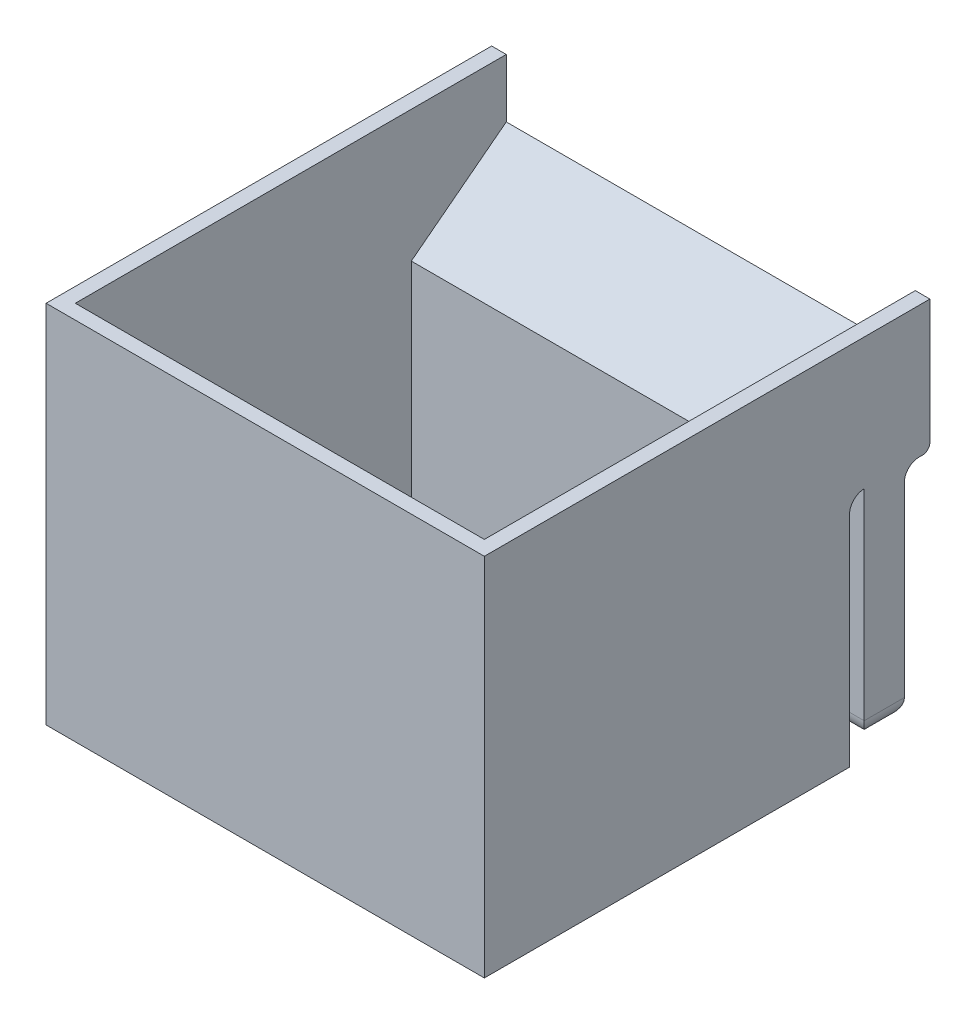
SolidWorks part; units mm, degrees
ref_plane "前基準面" through (0, 0, 0) normal (0, 0, 1) x (1, 0, 0)
ref_plane "上基準面" through (0, 0, 0) normal (0, 1, 0) x (1, 0, 0)
ref_plane "右基準面" through (0, 0, 0) normal (1, 0, 0) x (0, 0, -1)
sketch "草圖1" plane through (0, 0, 0) normal (1, 0, 0) x (0, 0, -1)
  line L0 (-42.2544, 29.5336) -> (-42.2544, -20.4664)
  line L1 (-42.2544, -20.4664) -> (7.7456, -20.4664)
  line L2 (7.7456, -20.4664) -> (7.7456, 11.5336)
  line L3 (7.7456, 11.5336) -> (18.7456, 11.5336)
  line L4 (18.7456, 11.5336) -> (18.7456, 21.5336)
  line L6 (5.7456, 11.5336) -> (5.7456, -18.4664)
  line L7 (5.7456, -18.4664) -> (-40.2544, -18.4664)
  line L8 (-40.2544, -18.4664) -> (-40.2544, 29.5336)
  line L9 (-40.2544, 29.5336) -> (-42.2544, 29.5336)
  line L10 (18.7456, 21.5336) -> (5.7456, 11.5336)
  dimension "D1" = 32
  dimension "D2" = 50
  dimension "D3" = 50
  dimension "D4" = 10
  dimension "D5" = 11
  dimension "D6" = 2
  dimension "D7" = 2
  dimension "D8" = 2
extrude "填料-伸長1" add sketch "草圖1" along normal blind 60
fillet "圓角1" radius 2 1 edges at (30, 11.5336, -7.7456)
sketch "草圖2" plane through (0, 11.5336, 0) normal (0, -1, 0) x (1, 0, 0)
  line L0 (60, -9.7456) -> (60, -18.7456) construction
  line L1 (0, -9.7456) -> (60, -9.7456)
  line L2 (0, -9.7456) -> (0, -15.2456)
  line L3 (0, -15.2456) -> (60, -15.2456)
  line L4 (60, -9.7456) -> (60, -15.2456)
  dimension "D1" = 5.5
extrude "填料-伸長2" add sketch "草圖2" along normal blind 30 contours L2 L1 L4 L3
fillet "圓角3" radius 2 1 edges at (30, 11.5336, -15.2456)
sketch "草圖3" plane through (0, -18.4664, 0) normal (0, 1, 0) x (1, 0, 0)
  line L0 (0, -27.5) -> (0, 27.5) construction
  line L1 (0, 5.7456) -> (2, 5.7456)
  line L2 (0, 5.7456) -> (0, -40.2544)
  line L3 (0, -40.2544) -> (2, -40.2544)
  line L4 (2, 5.7456) -> (2, -40.2544)
  line L5 (60, 5.7456) -> (0, 5.7456) construction
  line L6 (60, -40.2544) -> (0, -40.2544) construction
  line L8 (60, 5.7456) -> (58, 5.7456)
  line L9 (60, 5.7456) -> (60, -40.2544)
  line L10 (60, -40.2544) -> (58, -40.2544)
  line L11 (58, 5.7456) -> (58, -40.2544)
  line M3 (0, 5.7456) -> (0, -40.2544)
  line M4 (0, -40.2544) -> (60, -40.2544)
  line M5 (60, -40.2544) -> (60, 5.7456)
  line M6 (60, 5.7456) -> (0, 5.7456)
  dimension "D1" = 2
  dimension "D2" = 2
extrude "填料-伸長3" add sketch "草圖3" along normal blind 48 contours L4 M6 M3 M4 | L11 M6 M4 M5
sketch "草圖4" plane through (0, 0, -5.7456) normal (0, 0, -1) x (-1, 0, 0)
  line L0 (0, 27.5) -> (0, -27.5) construction
  line L1 (-2, 29.5336) -> (0, 29.5336)
  line L2 (-2, 29.5336) -> (-2, 11.5336)
  line L3 (-2, 11.5336) -> (0, 11.5336)
  line L4 (0, 29.5336) -> (0, 11.5336)
  dimension "D1" = 18
extrude "填料-伸長4" add sketch "草圖4" along normal blind 13
sketch "草圖5" plane through (0, 0, -5.7456) normal (0, 0, -1) x (-1, 0, 0)
  line L0 (-60, 11.5336) -> (0, 11.5336) construction
  line L1 (-60, 29.5336) -> (-58, 29.5336)
  line L2 (-60, 29.5336) -> (-60, 11.5336)
  line L3 (-60, 11.5336) -> (-58, 11.5336)
  line L4 (-58, 29.5336) -> (-58, 11.5336)
  line L5 (-58, 29.5336) -> (-58, -18.4664) construction
extrude "填料-伸長5" add sketch "草圖5" along normal blind 13
fillet "圓角4" radius 1 1 edges at (30, 11.5336, -18.7456)
fillet "圓角5" radius 2.5 4 edges at (0, -18.4664, -12.4956) (60, -18.4664, -12.4956) (30, -18.4664, -9.7456) (30, -18.4664, -15.2456)
